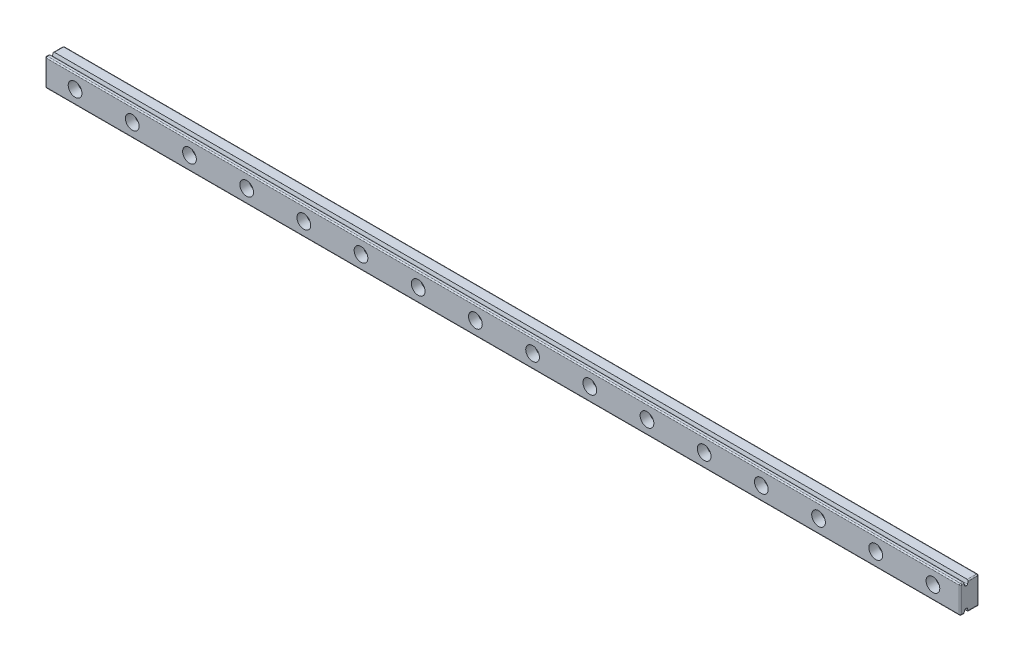
SolidWorks part; units mm, degrees
ref_plane "Front Plane" through (0, 0, 0) normal (0, 0, 1) x (1, 0, 0)
ref_plane "Top Plane" through (0, 0, 0) normal (0, 1, 0) x (1, 0, 0)
ref_plane "Right Plane" through (0, 0, 0) normal (1, 0, 0) x (0, 0, -1)
sketch "Sketch1" plane through (0, 0, 0) normal (1, 0, 0) x (0, 0, -1)
  line L0 (-0.5, 6) -> (4, 6)
  line L1 (-4, 6) -> (-2.5, 6)
  line L2 (-4, 6) -> (-4, -6)
  line L3 (-4, -6) -> (-2.5, -6)
  line L4 (4, 6) -> (4, -6)
  line L5 (-4, 6) -> (4, -6) construction
  line L6 (-4, -6) -> (4, 6) construction
  line L8 (-2.5, 6) -> (-2.5, 4.25)
  line L9 (-2.5, 4.25) -> (-0.5, 4.25)
  line L10 (-0.5, 6) -> (-0.5, 4.25)
  line L12 (-2.5, -6) -> (-2.5, -4.25)
  line L13 (-2.5, -4.25) -> (-0.5, -4.25)
  line L14 (-0.5, -6) -> (-0.5, -4.25)
  line L15 (-0.5, -6) -> (4, -6)
  point P0 (0, 0)
  dimension "D1" = 12
  dimension "D2" = 8
  dimension "D3" = 2
  dimension "D4" = 2
  dimension "D5" = 1.5
  dimension "D6" = 1.5
  dimension "D7" = 8.5
  dimension "D8" = 4.25
extrude "Boss-Extrude1" add sketch "Sketch1" along normal blind 400
sketch "Sketch2" plane through (0, 0, 4) normal (0, 0, 1) x (1, 0, 0)
  line L0 (0, 6) -> (0, -6) construction
  circle A0 centre (13, 0) radius 1.75
  circle A1 centre (38, 0) radius 1.75
  circle A2 centre (63, 0) radius 1.75
  circle A3 centre (88, 0) radius 1.75
  circle A4 centre (113, 0) radius 1.75
  circle A5 centre (138, 0) radius 1.75
  circle A6 centre (163, 0) radius 1.75
  circle A7 centre (188, 0) radius 1.75
  circle A8 centre (213, 0) radius 1.75
  circle A9 centre (238, 0) radius 1.75
  circle A10 centre (263, 0) radius 1.75
  circle A11 centre (288, 0) radius 1.75
  circle A12 centre (313, 0) radius 1.75
  circle A13 centre (338, 0) radius 1.75
  circle A14 centre (363, 0) radius 1.75
  circle A15 centre (388, 0) radius 1.75
  dimension "D1" = 3.5
  dimension "D2" = 13
  dimension "D3" = 16
extrude "Cut-Extrude1" cut sketch "Sketch2" against normal blind 10
sketch "Sketch3" plane through (0, 0, 4) normal (0, 0, 1) x (1, 0, 0)
  circle A0 centre (13, 0) radius 3
  circle A1 centre (38, 0) radius 3
  circle A2 centre (63, 0) radius 3
  circle A3 centre (88, 0) radius 3
  circle A4 centre (113, 0) radius 3
  circle A5 centre (138, 0) radius 3
  circle A6 centre (163, 0) radius 3
  circle A7 centre (188, 0) radius 3
  circle A8 centre (213, 0) radius 3
  circle A9 centre (238, 0) radius 3
  circle A10 centre (263, 0) radius 3
  circle A11 centre (288, 0) radius 3
  circle A12 centre (313, 0) radius 3
  circle A13 centre (338, 0) radius 3
  circle A14 centre (363, 0) radius 3
  circle A15 centre (388, 0) radius 3
  dimension "D1" = 6
  dimension "D2" = 16
extrude "Cut-Extrude2" cut sketch "Sketch3" against normal blind 4
chamfer "Chamfer1" distance 0.5 angle 74 4 edges at (200, -4.25, 2.5) (200, -4.25, 0.5) (200, 4.25, 2.5) (200, 4.25, 0.5)
fillet "Fillet1" radius 0.5 20 edges at (400, -6, -1.75) (400, 0, -4) (400, 6, -1.75) (400, 6, 3.25) (400, 0, 4) (400, -6, 3.25) (0, -6, 3.25) (0, -6, -1.75) (0, 0, -4) (0, 6, -1.75) (0, 6, 3.25) (0, 0, 4) (200, -4.25, 1) (200, -4.25, 2) (200, 4.25, 2) (200, 4.25, 1) (200, -6, 4) (200, 6, 4) (200, -6, -4) (200, 6, -4)
